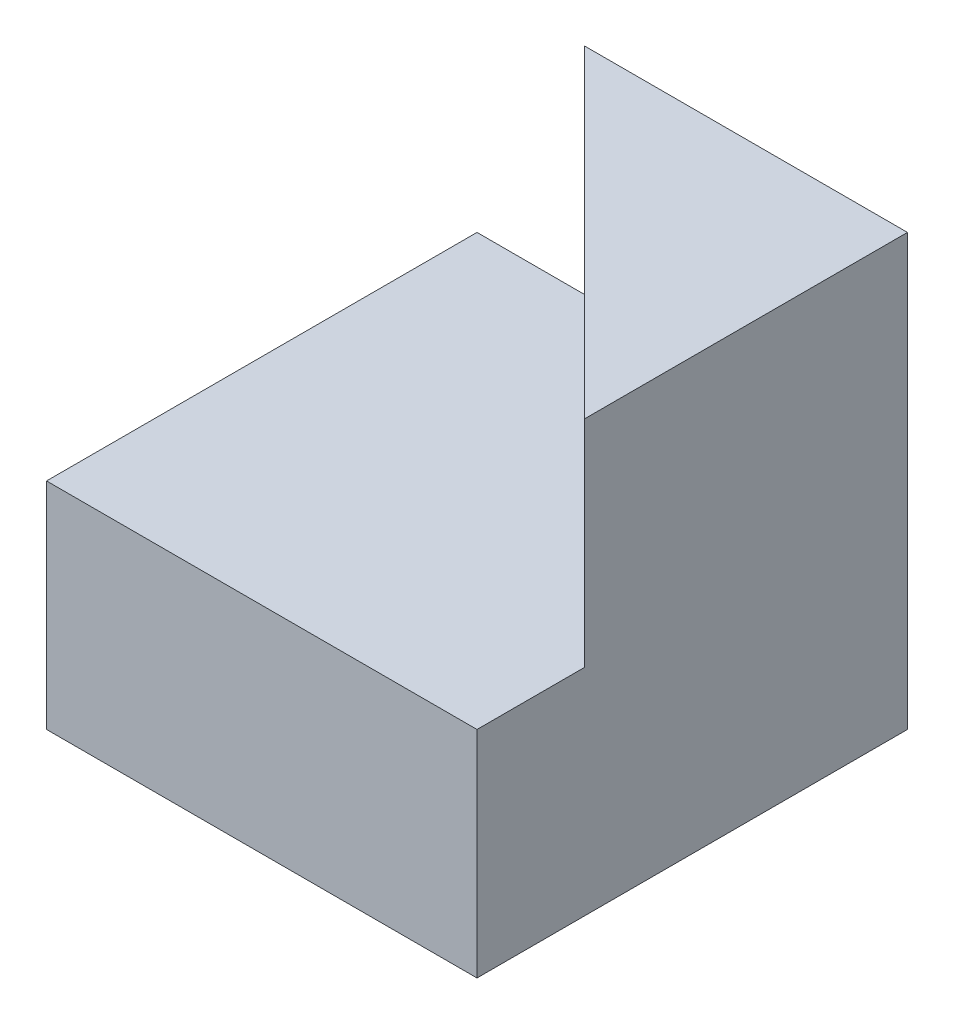
SolidWorks part; units mm, degrees
ref_plane "Front Plane" through (0, 0, 0) normal (0, 0, 1) x (1, 0, 0)
ref_plane "Top Plane" through (0, 0, 0) normal (0, 1, 0) x (1, 0, 0)
ref_plane "Right Plane" through (0, 0, 0) normal (1, 0, 0) x (0, 0, -1)
sketch "Sketch1" plane through (0, 0, 0) normal (0, 0, 1) x (1, 0, 0)
  line L1 (0, 0) -> (40, 0)
  line L2 (0, 0) -> (0, 40)
  line L3 (0, 40) -> (40, 40)
  line L4 (40, 0) -> (40, 40)
  dimension "D1" = 40
  dimension "D2" = 40
extrude "Boss-Extrude1" add sketch "Sketch1" along normal blind 40
sketch "Sketch2" plane through (0, 0, 40) normal (0, 0, 1) x (1, 0, 0)
  line L1 (0, 40) -> (10, 40)
  line L2 (0, 40) -> (0, 20)
  line L3 (0, 20) -> (10, 20)
  line L4 (10, 40) -> (10, 20)
  dimension "D1" = 10
  dimension "D2" = 20
extrude "Cut-Extrude1" cut sketch "Sketch2" against normal blind 40
sketch "Sketch3" plane through (0, 40, 0) normal (0, 1, 0) x (1, 0, 0)
  line L0 (10, 0) -> (40, -30)
  line L1 (40, 0) -> (10, 0) construction
  line L2 (40, -40) -> (40, 0) construction
  line L3 (40, -30) -> (40, 0)
  line L4 (40, 0) -> (10, 0)
  line L5 (10, 0) -> (10, -40)
  line L8 (10, -40) -> (40, -40)
  line L9 (40, -40) -> (40, -30)
  line M5 (10, 0) -> (10, -40)
  line M6 (10, -40) -> (40, -40)
  line M7 (40, -40) -> (40, 0)
  dimension "D1" = 30
  dimension "D2" = 30
  dimension "D3" = 40
extrude "Cut-Extrude3" cut sketch "Sketch3" against normal blind 20 contours L0 M5 M6 M7
